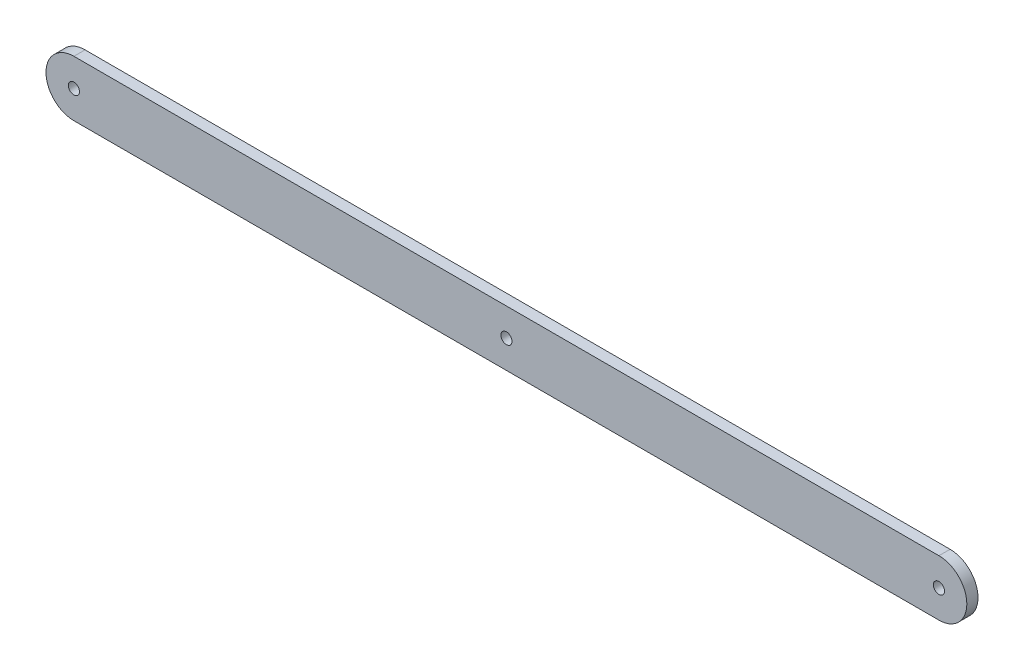
SolidWorks part; units mm, degrees
ref_plane "前视基准面" through (0, 0, 0) normal (0, 0, 1) x (1, 0, 0)
ref_plane "上视基准面" through (0, 0, 0) normal (0, 1, 0) x (1, 0, 0)
ref_plane "右视基准面" through (0, 0, 0) normal (1, 0, 0) x (0, 0, -1)
sketch "草图1" plane through (0, 0, 0) normal (0, 0, 1) x (1, 0, 0)
  line L0 (-102.381, 17.9762) -> (207.619, 17.9762)
  line L1 (207.619, 37.9762) -> (-102.381, 37.9762)
  arc A0 (-102.381, 37.9762) -> (-102.381, 17.9762) centre (-102.381, 27.9762) ccw
  arc A1 (207.619, 17.9762) -> (207.619, 37.9762) centre (207.619, 27.9762) ccw
  circle A2 centre (207.619, 27.9762) radius 2
  circle A3 centre (52.619, 27.9762) radius 2
  circle A4 centre (-102.381, 27.9762) radius 2
  dimension "D1" = 20
  dimension "D2" = 20
  dimension "D3" = 310
  dimension "D4" = 4
  dimension "D6" = 10
  dimension "D7" = 4
  dimension "D8" = 4
  dimension "D10" = 155
  dimension "D5" = 20
extrude "凸台-拉伸1" add sketch "草图1" along normal blind 4
